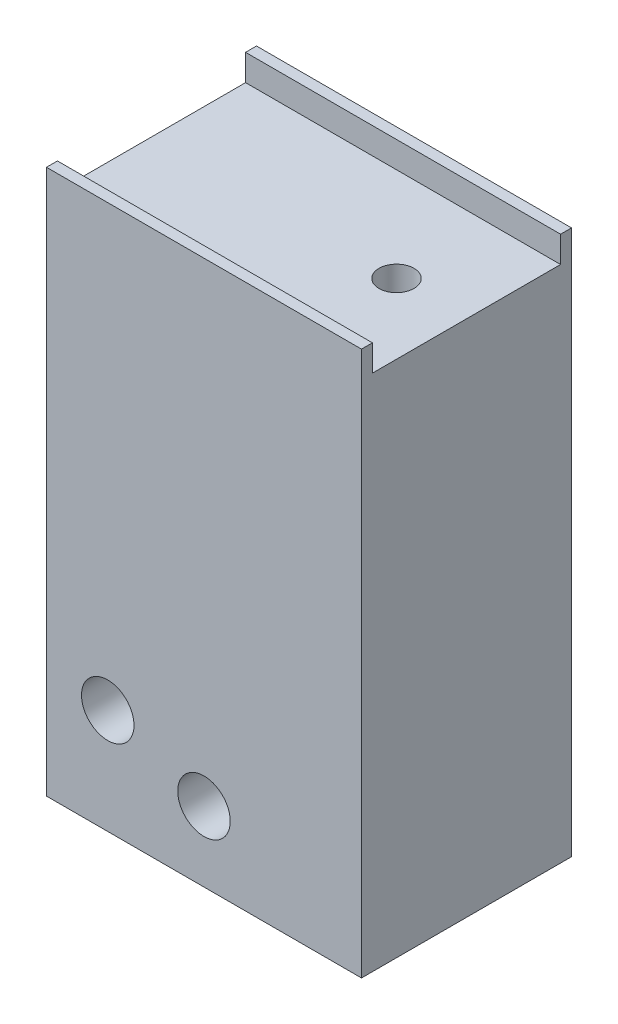
SolidWorks part; units mm, degrees
ref_plane "Front Plane" through (0, 0, 0) normal (0, 0, 1) x (1, 0, 0)
ref_plane "Top Plane" through (0, 0, 0) normal (0, 1, 0) x (1, 0, 0)
ref_plane "Right Plane" through (0, 0, 0) normal (1, 0, 0) x (0, 0, -1)
sketch "Sketch2" plane through (0, 0, 0) normal (1, 0, 0) x (0, 0, -1)
  line L2 (0, 0) -> (0, 10)
  line L3 (0, 10) -> (0.625, 10)
  line L4 (12, 0) -> (12, 10)
  line L5 (0.625, 10) -> (0.625, 8.5)
  line L6 (11.375, 10) -> (11.375, 8.5)
  line L7 (0.625, 8.5) -> (11.375, 8.5)
  line L8 (11.375, 10) -> (12, 10)
  line L13 (0, 0) -> (12, 0)
  dimension "D1" = 10.75
  dimension "D3" = 0.625
  dimension "D4" = 10
  dimension "D5" = 1.5
extrude "Boss-Extrude1" add sketch "Sketch2" along normal blind 8
sketch "Sketch3" plane through (0, 0, 0) normal (0, -1, 0) x (1, 0, 0)
  line L0 (8, 0) -> (0, 0) construction
  line L1 (8, 0) -> (8, -12) construction
  circle A0 centre (4, -6) radius 1
  point P5 (4, 0)
  point P9 (8, -6)
  dimension "D1" = 2
extrude "Cut-Extrude1" cut sketch "Sketch3" against normal up to next contours A0
sketch "Sketch6" plane through (0, 0, 0) normal (-1, 0, 0) x (0, 0, 1)
  line L8 (-12, 0) -> (0, 0)
  line L9 (0, 0) -> (0, 10)
  line L10 (0, 10) -> (-0.625, 10)
  line L11 (-0.625, 10) -> (-0.625, 8.5)
  line L12 (-0.625, 8.5) -> (-11.375, 8.5)
  line L13 (-11.375, 8.5) -> (-11.375, 10)
  line L14 (-11.375, 10) -> (-12, 10)
  line L15 (-12, 10) -> (-12, 0)
  line L16 (-12, 0) -> (0, 0)
  line L17 (0, 0) -> (0, 10)
  line L18 (0, 10) -> (-0.625, 10)
  line L19 (-0.625, 10) -> (-0.625, 8.5)
  line L20 (-0.625, 8.5) -> (-11.375, 8.5)
  line L21 (-11.375, 8.5) -> (-11.375, 10)
  line L22 (-11.375, 10) -> (-12, 10)
  line L23 (-12, 10) -> (-12, 0)
  dimension "D1" = 0
extrude "Boss-Extrude2" add sketch "Sketch6" along normal blind 10
sketch "Sketch7" plane through (0, 0, 0) normal (0, -1, 0) x (1, 0, 0)
  line L4 (8, 0) -> (-10, 0)
  line L5 (-10, 0) -> (-10, -12)
  line L6 (-10, -12) -> (8, -12)
  line L7 (8, -12) -> (8, 0)
  line L8 (8, 0) -> (-10, 0)
  line L9 (-10, 0) -> (-10, -12)
  line L10 (-10, -12) -> (8, -12)
  line L11 (8, -12) -> (8, 0)
  circle A0 centre (4, -6) radius 1 construction
  circle A1 centre (4, -6) radius 1
  dimension "D1" = 0
extrude "Boss-Extrude3" add sketch "Sketch7" along normal blind 21.12
sketch "Sketch11" plane through (0, 0, 0) normal (0, 0, 1) x (1, 0, 0)
  line L0 (8, -21.12) -> (-10, -21.12) construction
  line L1 (-10, -21.12) -> (-10, 10) construction
  line L2 (8, 10) -> (8, -21.12) construction
  circle A0 centre (-6.5, -15.12) radius 1.5
  circle A1 centre (-1, -17.12) radius 1.5
  point P8 (0, 0)
  point P11 (0, 0)
  point P12 (0, -17.7676)
  dimension "D1" = 3
  dimension "D2" = 3
  dimension "D3" = 6
  dimension "D4" = 3.5
  dimension "D5" = 9
  dimension "D6" = 4
extrude "Cut-Extrude4" cut sketch "Sketch11" against normal through all
